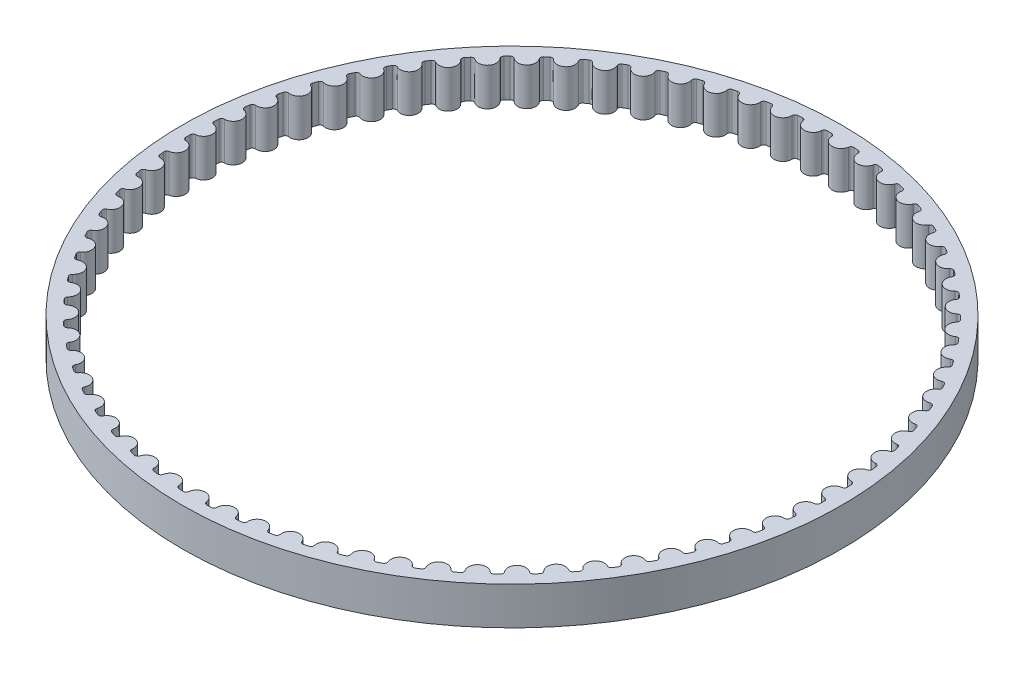
SolidWorks part; units mm, degrees
ref_plane "Front Plane" through (0, 0, 0) normal (0, 0, 1) x (1, 0, 0)
ref_plane "Top Plane" through (0, 0, 0) normal (0, 1, 0) x (1, 0, 0)
ref_plane "Right Plane" through (0, 0, 0) normal (1, 0, 0) x (0, 0, -1)
sketch "Sketch1" plane through (0, 0, 0) normal (0, 1, 0) x (1, 0, 0)
  circle A0 centre (0, 0) radius 34.819
  arc B0 (-1.7179, -33.475) -> (-1.2473, -33.4958) centre (0, 0) ccw
  arc B1 (-1.2473, -33.4958) -> (-0.9389, -33.2286) centre (-1.2362, -33.197) ccw
  arc B2 (0.9389, -33.2286) -> (-0.9389, -33.2286) centre (0, -33.3285) ccw
  arc B3 (0.9389, -33.2286) -> (1.2473, -33.4958) centre (1.2362, -33.197) ccw
  arc B4 (1.2473, -33.4958) -> (1.7179, -33.475) centre (0, 0) ccw
  arc B5 (1.7179, -33.475) -> (2.0015, -33.1816) centre (1.7026, -33.1763) ccw
  arc B6 (3.872, -33.0156) -> (2.0015, -33.1816) centre (2.9456, -33.1981) ccw
  arc B7 (3.872, -33.0156) -> (4.2028, -33.2545) centre (4.1653, -32.9578) ccw
  arc B8 (4.2028, -33.2545) -> (4.6697, -33.1921) centre (0, 0) ccw
  arc B9 (4.6697, -33.1921) -> (4.9263, -32.8748) centre (4.628, -32.896) ccw
  arc B10 (6.7747, -32.5442) -> (4.9263, -32.8748) centre (5.8681, -32.8078) ccw
  arc B11 (6.7747, -32.5442) -> (7.1254, -32.7529) centre (7.0619, -32.4607) ccw
  arc B12 (7.1254, -32.7529) -> (7.5849, -32.6495) centre (0, 0) ccw
  arc B13 (7.5849, -32.6495) -> (7.8125, -32.3108) centre (7.5173, -32.3583) ccw
  arc B14 (9.6245, -31.8181) -> (7.8125, -32.3108) centre (8.7447, -32.1608) ccw
  arc B15 (9.6245, -31.8181) -> (9.9922, -31.995) centre (9.9031, -31.7096) ccw
  arc B16 (9.9922, -31.995) -> (10.4408, -31.8514) centre (0, 0) ccw
  arc B17 (10.4408, -31.8514) -> (10.6375, -31.4939) centre (10.3477, -31.5673) ccw
  arc B18 (12.3989, -30.843) -> (10.6375, -31.4939) centre (11.5529, -31.2621) ccw
  arc B19 (12.3989, -30.843) -> (12.7809, -30.9867) centre (12.6668, -30.7103) ccw
  arc B20 (12.7809, -30.9867) -> (13.215, -30.804) centre (0, 0) ccw
  arc B21 (13.215, -30.804) -> (13.3794, -30.4305) centre (13.0971, -30.5292) ccw
  arc B22 (15.0763, -29.6265) -> (13.3794, -30.4305) centre (14.2706, -30.1188) ccw
  arc B23 (15.0763, -29.6265) -> (15.4694, -29.7358) centre (15.3315, -29.4706) ccw
  arc B24 (15.4694, -29.7358) -> (15.8858, -29.5155) centre (0, 0) ccw
  arc B25 (15.8858, -29.5155) -> (16.0164, -29.129) centre (15.744, -29.2522) ccw
  arc B26 (17.6357, -28.1781) -> (16.0164, -29.129) centre (16.8767, -28.7397) ccw
  arc B27 (17.6357, -28.1781) -> (18.037, -28.2523) centre (17.8761, -28.0003) ccw
  arc B28 (18.037, -28.2523) -> (18.4322, -27.996) centre (0, 0) ccw
  arc B29 (18.4322, -27.996) -> (18.5282, -27.5994) centre (18.2678, -27.7463) ccw
  arc B30 (20.0571, -26.5092) -> (18.5282, -27.5994) centre (19.3506, -27.1356) ccw
  arc B31 (20.0571, -26.5092) -> (20.4633, -26.5476) centre (20.2808, -26.3108) ccw
  arc B32 (20.4633, -26.5476) -> (20.8343, -26.2575) centre (0, 0) ccw
  arc B33 (20.8343, -26.2575) -> (20.8949, -25.8539) centre (20.6485, -26.0232) ccw
  arc B34 (22.3215, -24.6328) -> (20.8949, -25.8539) centre (21.6732, -25.3192) ccw
  arc B35 (22.3215, -24.6328) -> (22.7295, -24.6352) centre (22.5268, -24.4154) ccw
  arc B36 (22.7295, -24.6352) -> (23.0734, -24.3134) centre (0, 0) ccw
  arc B37 (23.0734, -24.3134) -> (23.0981, -23.906) centre (22.8676, -24.0965) ccw
  arc B38 (24.4112, -22.5636) -> (23.0981, -23.906) centre (23.8261, -23.3047) ccw
  arc B39 (24.4112, -22.5636) -> (24.8178, -22.5299) centre (24.5965, -22.329) ccw
  arc B40 (24.8178, -22.5299) -> (25.132, -22.179) centre (0, 0) ccw
  arc B41 (25.132, -22.179) -> (25.1206, -21.7711) centre (24.9078, -21.9811) ccw
  arc B42 (26.3098, -20.3179) -> (25.1206, -21.7711) centre (25.7925, -21.1077) ccw
  arc B43 (26.3098, -20.3179) -> (26.7119, -20.2484) centre (26.4736, -20.0677) ccw
  arc B44 (26.7119, -20.2484) -> (26.9938, -19.871) centre (0, 0) ccw
  arc B45 (26.9938, -19.871) -> (26.9464, -19.4657) centre (26.753, -19.6938) ccw
  arc B46 (28.0026, -17.9131) -> (26.9464, -19.4657) centre (27.5571, -18.7456) ccw
  arc B47 (28.0026, -17.9131) -> (28.397, -17.8083) centre (28.1436, -17.6495) ccw
  arc B48 (28.397, -17.8083) -> (28.6444, -17.4076) centre (0, 0) ccw
  arc B49 (28.6444, -17.4076) -> (28.5613, -17.008) centre (28.3889, -17.2523) ccw
  arc B50 (29.4761, -15.3681) -> (28.5613, -17.008) centre (29.106, -16.2367) ccw
  arc B51 (29.4761, -15.3681) -> (29.8597, -15.2289) centre (29.5934, -15.0931) ccw
  arc B52 (29.8597, -15.2289) -> (30.0708, -14.8078) centre (0, 0) ccw
  arc B53 (30.0708, -14.8078) -> (29.9527, -14.4172) centre (29.8025, -14.6758) ccw
  arc B54 (30.719, -12.7029) -> (29.9527, -14.4172) centre (30.4271, -13.6008) ccw
  arc B55 (30.719, -12.7029) -> (31.0888, -12.5303) centre (30.8115, -12.4185) ccw
  arc B56 (31.0888, -12.5303) -> (31.2618, -12.0922) centre (0, 0) ccw
  arc B57 (31.2618, -12.0922) -> (31.1097, -11.7136) centre (30.983, -11.9844) ccw
  arc B58 (31.7215, -9.9382) -> (31.1097, -11.7136) centre (31.5101, -10.8584) ccw
  arc B59 (31.7215, -9.9382) -> (32.0746, -9.7337) centre (31.7885, -9.6468) ccw
  arc B60 (32.0746, -9.7337) -> (32.2082, -9.282) centre (0, 0) ccw
  arc B61 (32.2082, -9.282) -> (32.0232, -8.9183) centre (31.9209, -9.1992) ccw
  arc B62 (32.4757, -7.0958) -> (32.0232, -8.9183) centre (32.3464, -8.0311) ccw
  arc B63 (32.4757, -7.0958) -> (32.8093, -6.8608) centre (32.5167, -6.7996) ccw
  arc B64 (32.8093, -6.8608) -> (32.9025, -6.3991) centre (0, 0) ccw
  arc B65 (32.9025, -6.3991) -> (32.6861, -6.0531) centre (32.609, -6.342) ccw
  arc B66 (32.9758, -4.1978) -> (32.6861, -6.0531) centre (32.9296, -5.1409) ccw
  arc B67 (32.9758, -4.1978) -> (33.2873, -3.9343) centre (32.9904, -3.8992) ccw
  arc B68 (33.2873, -3.9343) -> (33.3393, -3.4661) centre (0, 0) ccw
  arc B69 (33.3393, -3.4661) -> (33.0932, -3.1407) centre (33.0419, -3.4352) ccw
  arc B70 (33.2177, -1.267) -> (33.0932, -3.1407) centre (33.2551, -2.2104) ccw
  arc B71 (33.2177, -1.267) -> (33.5048, -0.9769) centre (33.2059, -0.9682) ccw
  arc B72 (33.5048, -0.9769) -> (33.5152, -0.506) centre (0, 0) ccw
  arc B73 (33.5152, -0.506) -> (33.2413, -0.2036) centre (33.2162, -0.5015) ccw
  arc B74 (33.1997, 1.6738) -> (33.2413, -0.2036) centre (33.3203, 0.7373) ccw
  arc B75 (33.1997, 1.6738) -> (33.46, 1.988) centre (33.1615, 1.9703) ccw
  arc B76 (33.46, 1.988) -> (33.4288, 2.458) centre (0, 0) ccw
  arc B77 (33.4288, 2.458) -> (33.1292, 2.7351) centre (33.1306, 2.4361) ccw
  arc B78 (32.9219, 4.6014) -> (33.1292, 2.7351) centre (33.1248, 3.6793) ccw
  arc B79 (32.9219, 4.6014) -> (33.1534, 4.9375) centre (32.8576, 4.8934) ccw
  arc B80 (33.1534, 4.9375) -> (33.0807, 5.4028) centre (0, 0) ccw
  arc B81 (33.0807, 5.4028) -> (32.7578, 5.6523) centre (32.7856, 5.3546) ccw
  arc B82 (32.3864, 7.493) -> (32.7578, 5.6523) centre (32.67, 6.5924) ccw
  arc B83 (32.3864, 7.493) -> (32.5872, 7.8482) centre (32.2966, 7.7782) ccw
  arc B84 (32.5872, 7.8482) -> (32.4738, 8.3054) centre (0, 0) ccw
  arc B85 (32.4738, 8.3054) -> (32.1301, 8.5254) centre (32.1841, 8.2313) ccw
  arc B86 (31.5974, 10.326) -> (32.1301, 8.5254) centre (31.9595, 9.454) ccw
  arc B87 (31.5974, 10.326) -> (31.7661, 10.6976) centre (31.4827, 10.6022) ccw
  arc B88 (31.7661, 10.6976) -> (31.6126, 11.1429) centre (0, 0) ccw
  arc B89 (31.6126, 11.1429) -> (31.2509, 11.3317) centre (31.3307, 11.0435) ccw
  arc B90 (30.5611, 13.0782) -> (31.2509, 11.3317) centre (30.9989, 12.2416) ccw
  arc B91 (30.5611, 13.0782) -> (30.6963, 13.4632) centre (30.4225, 13.3431) ccw
  arc B92 (30.6963, 13.4632) -> (30.5041, 13.8932) centre (0, 0) ccw
  arc B93 (30.5041, 13.8932) -> (30.1271, 14.0493) centre (30.232, 13.7693) ccw
  arc B94 (29.2857, 15.728) -> (30.1271, 14.0493) centre (29.7957, 14.9334) ccw
  arc B95 (29.2857, 15.728) -> (29.3863, 16.1235) centre (29.1242, 15.9797) ccw
  arc B96 (29.3863, 16.1235) -> (29.1569, 16.5348) centre (0, 0) ccw
  arc B97 (29.1569, 16.5348) -> (28.7675, 16.6569) centre (28.8968, 16.3873) ccw
  arc B98 (27.7811, 18.2547) -> (28.7675, 16.6569) centre (28.3593, 17.5083) ccw
  arc B99 (27.7811, 18.2547) -> (27.8464, 18.6576) centre (27.598, 18.4911) ccw
  arc B100 (27.8464, 18.6576) -> (27.5814, 19.047) centre (0, 0) ccw
  arc B101 (27.5814, 19.047) -> (27.1828, 19.1342) centre (27.3354, 18.8771) ccw
  arc B102 (26.059, 20.6386) -> (27.1828, 19.1342) centre (26.7009, 19.9462) ccw
  arc B103 (26.059, 20.6386) -> (26.0884, 21.0456) centre (25.8557, 20.8579) ccw
  arc B104 (26.0884, 21.0456) -> (25.7901, 21.4101) centre (0, 0) ccw
  arc B105 (25.7901, 21.4101) -> (25.3853, 21.4618) centre (25.5601, 21.2191) ccw
  arc B106 (24.133, 22.8609) -> (25.3853, 21.4618) centre (24.8336, 22.228) ccw
  arc B107 (24.133, 22.8609) -> (24.1263, 23.2689) centre (23.9111, 23.0614) ccw
  arc B108 (24.1263, 23.2689) -> (23.797, 23.6057) centre (0, 0) ccw
  arc B109 (23.797, 23.6057) -> (23.3892, 23.6213) centre (23.5847, 23.3951) ccw
  arc B110 (22.0181, 24.9044) -> (23.3892, 23.6213) centre (22.7719, 24.3358) ccw
  arc B111 (22.0181, 24.9044) -> (21.9754, 25.3102) centre (21.7794, 25.0844) ccw
  arc B112 (21.9754, 25.3102) -> (21.6176, 25.6165) centre (0, 0) ccw
  arc B113 (21.6176, 25.6165) -> (21.21, 25.596) centre (21.4248, 25.388) ccw
  arc B114 (19.7309, 26.7529) -> (21.21, 25.596) centre (20.532, 26.2531) ccw
  arc B115 (19.7309, 26.7529) -> (19.6525, 27.1533) centre (19.4772, 26.9111) ccw
  arc B116 (19.6525, 27.1533) -> (19.269, 27.4268) centre (0, 0) ccw
  arc B117 (19.269, 27.4268) -> (18.8649, 27.3704) centre (19.0971, 27.1821) ccw
  arc B118 (17.2892, 28.392) -> (18.8649, 27.3704) centre (18.1314, 27.965) ccw
  arc B119 (17.2892, 28.392) -> (17.1758, 28.784) centre (17.0226, 28.5272) ccw
  arc B120 (17.1758, 28.784) -> (16.7696, 29.0225) centre (0, 0) ccw
  arc B121 (16.7696, 29.0225) -> (16.372, 28.9306) centre (16.62, 28.7636) ccw
  arc B122 (14.7123, 29.8089) -> (16.372, 28.9306) centre (15.5889, 29.458) ccw
  arc B123 (14.7123, 29.8089) -> (14.5646, 30.1893) centre (14.4347, 29.92) ccw
  arc B124 (14.5646, 30.1893) -> (14.139, 30.391) centre (0, 0) ccw
  arc B125 (14.139, 30.391) -> (13.7511, 30.2643) centre (14.0129, 30.1199) ccw
  arc B126 (12.0202, 30.9925) -> (13.7511, 30.2643) centre (12.9244, 30.7205) ccw
  arc B127 (12.0202, 30.9925) -> (11.8395, 31.3584) centre (11.7339, 31.0787) ccw
  arc B128 (11.8395, 31.3584) -> (11.3977, 31.5217) centre (0, 0) ccw
  arc B129 (11.3977, 31.5217) -> (11.0225, 31.3612) centre (11.296, 31.2405) ccw
  arc B130 (9.2341, 31.9336) -> (11.0225, 31.3612) centre (10.1587, 31.7426) ccw
  arc B131 (9.2341, 31.9336) -> (9.0217, 32.2821) centre (8.9412, 31.9941) ccw
  arc B132 (9.0217, 32.2821) -> (8.5672, 32.4057) centre (0, 0) ccw
  arc B133 (8.5672, 32.4057) -> (8.2077, 32.2127) centre (8.4908, 32.1166) ccw
  arc B134 (6.3756, 32.6247) -> (8.2077, 32.2127) centre (7.3136, 32.5162) ccw
  arc B135 (6.3756, 32.6247) -> (6.1333, 32.9531) centre (6.0786, 32.6591) ccw
  arc B136 (6.1333, 32.9531) -> (5.6697, 33.036) centre (0, 0) ccw
  arc B137 (5.6697, 33.036) -> (5.3286, 32.812) centre (5.6191, 32.7413) ccw
  arc B138 (3.4673, 33.0606) -> (5.3286, 32.812) centre (4.4112, 33.0353) ccw
  arc B139 (3.4673, 33.0606) -> (3.1969, 33.3662) centre (3.1684, 33.0686) ccw
  arc B140 (3.1969, 33.3662) -> (2.7278, 33.4078) centre (0, 0) ccw
  arc B141 (2.7278, 33.4078) -> (2.4078, 33.1546) centre (2.7034, 33.1098) ccw
  arc B142 (0.5318, 33.2376) -> (2.4078, 33.1546) centre (1.4742, 33.2959) ccw
  arc B143 (0.5318, 33.2376) -> (0.2355, 33.5182) centre (0.2334, 33.2192) ccw
  arc B144 (0.2355, 33.5182) -> (-0.2355, 33.5182) centre (0, 0) ccw
  arc B145 (-0.2355, 33.5182) -> (-0.5318, 33.2376) centre (-0.2334, 33.2192) ccw
  arc B146 (-2.4078, 33.1546) -> (-0.5318, 33.2376) centre (-1.4742, 33.2959) ccw
  arc B147 (-2.4078, 33.1546) -> (-2.7278, 33.4078) centre (-2.7034, 33.1098) ccw
  arc B148 (-2.7278, 33.4078) -> (-3.1969, 33.3662) centre (0, 0) ccw
  arc B149 (-3.1969, 33.3662) -> (-3.4673, 33.0606) centre (-3.1684, 33.0686) ccw
  arc B150 (-5.3286, 32.812) -> (-3.4673, 33.0606) centre (-4.4112, 33.0353) ccw
  arc B151 (-5.3286, 32.812) -> (-5.6697, 33.036) centre (-5.6191, 32.7413) ccw
  arc B152 (-5.6697, 33.036) -> (-6.1333, 32.9531) centre (0, 0) ccw
  arc B153 (-6.1333, 32.9531) -> (-6.3756, 32.6247) centre (-6.0786, 32.6591) ccw
  arc B154 (-8.2077, 32.2127) -> (-6.3756, 32.6247) centre (-7.3136, 32.5162) ccw
  arc B155 (-8.2077, 32.2127) -> (-8.5672, 32.4057) centre (-8.4908, 32.1166) ccw
  arc B156 (-8.5672, 32.4057) -> (-9.0217, 32.2821) centre (0, 0) ccw
  arc B157 (-9.0217, 32.2821) -> (-9.2341, 31.9336) centre (-8.9412, 31.9941) ccw
  arc B158 (-11.0225, 31.3612) -> (-9.2341, 31.9336) centre (-10.1587, 31.7426) ccw
  arc B159 (-11.0225, 31.3612) -> (-11.3977, 31.5217) centre (-11.296, 31.2405) ccw
  arc B160 (-11.3977, 31.5217) -> (-11.8395, 31.3584) centre (0, 0) ccw
  arc B161 (-11.8395, 31.3584) -> (-12.0202, 30.9925) centre (-11.7339, 31.0787) ccw
  arc B162 (-13.7511, 30.2643) -> (-12.0202, 30.9925) centre (-12.9244, 30.7205) ccw
  arc B163 (-13.7511, 30.2643) -> (-14.139, 30.391) centre (-14.0129, 30.1199) ccw
  arc B164 (-14.139, 30.391) -> (-14.5646, 30.1893) centre (0, 0) ccw
  arc B165 (-14.5646, 30.1893) -> (-14.7123, 29.8089) centre (-14.4347, 29.92) ccw
  arc B166 (-16.372, 28.9306) -> (-14.7123, 29.8089) centre (-15.5889, 29.458) ccw
  arc B167 (-16.372, 28.9306) -> (-16.7696, 29.0225) centre (-16.62, 28.7636) ccw
  arc B168 (-16.7696, 29.0225) -> (-17.1758, 28.784) centre (0, 0) ccw
  arc B169 (-17.1758, 28.784) -> (-17.2892, 28.392) centre (-17.0226, 28.5272) ccw
  arc B170 (-18.8649, 27.3704) -> (-17.2892, 28.392) centre (-18.1314, 27.965) ccw
  arc B171 (-18.8649, 27.3704) -> (-19.269, 27.4268) centre (-19.0971, 27.1821) ccw
  arc B172 (-19.269, 27.4268) -> (-19.6525, 27.1533) centre (0, 0) ccw
  arc B173 (-19.6525, 27.1533) -> (-19.7309, 26.7529) centre (-19.4772, 26.9111) ccw
  arc B174 (-21.21, 25.596) -> (-19.7309, 26.7529) centre (-20.532, 26.2531) ccw
  arc B175 (-21.21, 25.596) -> (-21.6176, 25.6165) centre (-21.4248, 25.388) ccw
  arc B176 (-21.6176, 25.6165) -> (-21.9754, 25.3102) centre (0, 0) ccw
  arc B177 (-21.9754, 25.3102) -> (-22.0181, 24.9044) centre (-21.7794, 25.0844) ccw
  arc B178 (-23.3892, 23.6213) -> (-22.0181, 24.9044) centre (-22.7719, 24.3358) ccw
  arc B179 (-23.3892, 23.6213) -> (-23.797, 23.6057) centre (-23.5847, 23.3951) ccw
  arc B180 (-23.797, 23.6057) -> (-24.1263, 23.2689) centre (0, 0) ccw
  arc B181 (-24.1263, 23.2689) -> (-24.133, 22.8609) centre (-23.9111, 23.0614) ccw
  arc B182 (-25.3853, 21.4618) -> (-24.133, 22.8609) centre (-24.8336, 22.228) ccw
  arc B183 (-25.3853, 21.4618) -> (-25.7901, 21.4101) centre (-25.5601, 21.2191) ccw
  arc B184 (-25.7901, 21.4101) -> (-26.0884, 21.0456) centre (0, 0) ccw
  arc B185 (-26.0884, 21.0456) -> (-26.059, 20.6386) centre (-25.8557, 20.8579) ccw
  arc B186 (-27.1828, 19.1342) -> (-26.059, 20.6386) centre (-26.7009, 19.9462) ccw
  arc B187 (-27.1828, 19.1342) -> (-27.5814, 19.047) centre (-27.3354, 18.8771) ccw
  arc B188 (-27.5814, 19.047) -> (-27.8464, 18.6576) centre (0, 0) ccw
  arc B189 (-27.8464, 18.6576) -> (-27.7811, 18.2547) centre (-27.598, 18.4911) ccw
  arc B190 (-28.7675, 16.6569) -> (-27.7811, 18.2547) centre (-28.3593, 17.5083) ccw
  arc B191 (-28.7675, 16.6569) -> (-29.1569, 16.5348) centre (-28.8968, 16.3873) ccw
  arc B192 (-29.1569, 16.5348) -> (-29.3863, 16.1235) centre (0, 0) ccw
  arc B193 (-29.3863, 16.1235) -> (-29.2857, 15.728) centre (-29.1242, 15.9797) ccw
  arc B194 (-30.1271, 14.0493) -> (-29.2857, 15.728) centre (-29.7957, 14.9334) ccw
  arc B195 (-30.1271, 14.0493) -> (-30.5041, 13.8932) centre (-30.232, 13.7693) ccw
  arc B196 (-30.5041, 13.8932) -> (-30.6963, 13.4632) centre (0, 0) ccw
  arc B197 (-30.6963, 13.4632) -> (-30.5611, 13.0782) centre (-30.4225, 13.3431) ccw
  arc B198 (-31.2509, 11.3317) -> (-30.5611, 13.0782) centre (-30.9989, 12.2416) ccw
  arc B199 (-31.2509, 11.3317) -> (-31.6126, 11.1429) centre (-31.3307, 11.0435) ccw
  arc B200 (-31.6126, 11.1429) -> (-31.7661, 10.6976) centre (0, 0) ccw
  arc B201 (-31.7661, 10.6976) -> (-31.5974, 10.326) centre (-31.4827, 10.6022) ccw
  arc B202 (-32.1301, 8.5254) -> (-31.5974, 10.326) centre (-31.9595, 9.454) ccw
  arc B203 (-32.1301, 8.5254) -> (-32.4738, 8.3054) centre (-32.1841, 8.2313) ccw
  arc B204 (-32.4738, 8.3054) -> (-32.5872, 7.8482) centre (0, 0) ccw
  arc B205 (-32.5872, 7.8482) -> (-32.3864, 7.493) centre (-32.2966, 7.7782) ccw
  arc B206 (-32.7578, 5.6523) -> (-32.3864, 7.493) centre (-32.67, 6.5924) ccw
  arc B207 (-32.7578, 5.6523) -> (-33.0807, 5.4028) centre (-32.7856, 5.3546) ccw
  arc B208 (-33.0807, 5.4028) -> (-33.1534, 4.9375) centre (0, 0) ccw
  arc B209 (-33.1534, 4.9375) -> (-32.9219, 4.6014) centre (-32.8576, 4.8934) ccw
  arc B210 (-33.1292, 2.7351) -> (-32.9219, 4.6014) centre (-33.1248, 3.6793) ccw
  arc B211 (-33.1292, 2.7351) -> (-33.4288, 2.458) centre (-33.1306, 2.4361) ccw
  arc B212 (-33.4288, 2.458) -> (-33.46, 1.988) centre (0, 0) ccw
  arc B213 (-33.46, 1.988) -> (-33.1997, 1.6738) centre (-33.1615, 1.9703) ccw
  arc B214 (-33.2413, -0.2036) -> (-33.1997, 1.6738) centre (-33.3203, 0.7373) ccw
  arc B215 (-33.2413, -0.2036) -> (-33.5152, -0.506) centre (-33.2162, -0.5015) ccw
  arc B216 (-33.5152, -0.506) -> (-33.5048, -0.9769) centre (0, 0) ccw
  arc B217 (-33.5048, -0.9769) -> (-33.2177, -1.267) centre (-33.2059, -0.9682) ccw
  arc B218 (-33.0932, -3.1407) -> (-33.2177, -1.267) centre (-33.2551, -2.2104) ccw
  arc B219 (-33.0932, -3.1407) -> (-33.3393, -3.4661) centre (-33.0419, -3.4352) ccw
  arc B220 (-33.3393, -3.4661) -> (-33.2873, -3.9343) centre (0, 0) ccw
  arc B221 (-33.2873, -3.9343) -> (-32.9758, -4.1978) centre (-32.9904, -3.8992) ccw
  arc B222 (-32.6861, -6.0531) -> (-32.9758, -4.1978) centre (-32.9296, -5.1409) ccw
  arc B223 (-32.6861, -6.0531) -> (-32.9025, -6.3991) centre (-32.609, -6.342) ccw
  arc B224 (-32.9025, -6.3991) -> (-32.8093, -6.8608) centre (0, 0) ccw
  arc B225 (-32.8093, -6.8608) -> (-32.4757, -7.0958) centre (-32.5167, -6.7996) ccw
  arc B226 (-32.0232, -8.9183) -> (-32.4757, -7.0958) centre (-32.3464, -8.0311) ccw
  arc B227 (-32.0232, -8.9183) -> (-32.2082, -9.282) centre (-31.9209, -9.1992) ccw
  arc B228 (-32.2082, -9.282) -> (-32.0746, -9.7337) centre (0, 0) ccw
  arc B229 (-32.0746, -9.7337) -> (-31.7215, -9.9382) centre (-31.7885, -9.6468) ccw
  arc B230 (-31.1097, -11.7136) -> (-31.7215, -9.9382) centre (-31.5101, -10.8584) ccw
  arc B231 (-31.1097, -11.7136) -> (-31.2618, -12.0922) centre (-30.983, -11.9844) ccw
  arc B232 (-31.2618, -12.0922) -> (-31.0888, -12.5303) centre (0, 0) ccw
  arc B233 (-31.0888, -12.5303) -> (-30.719, -12.7029) centre (-30.8115, -12.4185) ccw
  arc B234 (-29.9527, -14.4172) -> (-30.719, -12.7029) centre (-30.4271, -13.6008) ccw
  arc B235 (-29.9527, -14.4172) -> (-30.0708, -14.8078) centre (-29.8025, -14.6758) ccw
  arc B236 (-30.0708, -14.8078) -> (-29.8597, -15.2289) centre (0, 0) ccw
  arc B237 (-29.8597, -15.2289) -> (-29.4761, -15.3681) centre (-29.5934, -15.0931) ccw
  arc B238 (-28.5613, -17.008) -> (-29.4761, -15.3681) centre (-29.106, -16.2367) ccw
  arc B239 (-28.5613, -17.008) -> (-28.6444, -17.4076) centre (-28.3889, -17.2523) ccw
  arc B240 (-28.6444, -17.4076) -> (-28.397, -17.8083) centre (0, 0) ccw
  arc B241 (-28.397, -17.8083) -> (-28.0026, -17.9131) centre (-28.1436, -17.6495) ccw
  arc B242 (-26.9464, -19.4657) -> (-28.0026, -17.9131) centre (-27.5571, -18.7456) ccw
  arc B243 (-26.9464, -19.4657) -> (-26.9938, -19.871) centre (-26.753, -19.6938) ccw
  arc B244 (-26.9938, -19.871) -> (-26.7119, -20.2484) centre (0, 0) ccw
  arc B245 (-26.7119, -20.2484) -> (-26.3098, -20.3179) centre (-26.4736, -20.0677) ccw
  arc B246 (-25.1206, -21.7711) -> (-26.3098, -20.3179) centre (-25.7925, -21.1077) ccw
  arc B247 (-25.1206, -21.7711) -> (-25.132, -22.179) centre (-24.9078, -21.9811) ccw
  arc B248 (-25.132, -22.179) -> (-24.8178, -22.5299) centre (0, 0) ccw
  arc B249 (-24.8178, -22.5299) -> (-24.4112, -22.5636) centre (-24.5965, -22.329) ccw
  arc B250 (-23.0981, -23.906) -> (-24.4112, -22.5636) centre (-23.8261, -23.3047) ccw
  arc B251 (-23.0981, -23.906) -> (-23.0734, -24.3134) centre (-22.8676, -24.0965) ccw
  arc B252 (-23.0734, -24.3134) -> (-22.7295, -24.6352) centre (0, 0) ccw
  arc B253 (-22.7295, -24.6352) -> (-22.3215, -24.6328) centre (-22.5268, -24.4154) ccw
  arc B254 (-20.8949, -25.8539) -> (-22.3215, -24.6328) centre (-21.6732, -25.3192) ccw
  arc B255 (-20.8949, -25.8539) -> (-20.8343, -26.2575) centre (-20.6485, -26.0232) ccw
  arc B256 (-20.8343, -26.2575) -> (-20.4633, -26.5476) centre (0, 0) ccw
  arc B257 (-20.4633, -26.5476) -> (-20.0571, -26.5092) centre (-20.2808, -26.3108) ccw
  arc B258 (-18.5282, -27.5994) -> (-20.0571, -26.5092) centre (-19.3506, -27.1356) ccw
  arc B259 (-18.5282, -27.5994) -> (-18.4322, -27.996) centre (-18.2678, -27.7463) ccw
  arc B260 (-18.4322, -27.996) -> (-18.037, -28.2523) centre (0, 0) ccw
  arc B261 (-18.037, -28.2523) -> (-17.6357, -28.1781) centre (-17.8761, -28.0003) ccw
  arc B262 (-16.0164, -29.129) -> (-17.6357, -28.1781) centre (-16.8767, -28.7397) ccw
  arc B263 (-16.0164, -29.129) -> (-15.8858, -29.5155) centre (-15.744, -29.2522) ccw
  arc B264 (-15.8858, -29.5155) -> (-15.4694, -29.7358) centre (0, 0) ccw
  arc B265 (-15.4694, -29.7358) -> (-15.0763, -29.6265) centre (-15.3315, -29.4706) ccw
  arc B266 (-13.3794, -30.4305) -> (-15.0763, -29.6265) centre (-14.2706, -30.1188) ccw
  arc B267 (-13.3794, -30.4305) -> (-13.215, -30.804) centre (-13.0971, -30.5292) ccw
  arc B268 (-13.215, -30.804) -> (-12.7809, -30.9867) centre (0, 0) ccw
  arc B269 (-12.7809, -30.9867) -> (-12.3989, -30.843) centre (-12.6668, -30.7103) ccw
  arc B270 (-10.6375, -31.4939) -> (-12.3989, -30.843) centre (-11.5529, -31.2621) ccw
  arc B271 (-10.6375, -31.4939) -> (-10.4408, -31.8514) centre (-10.3477, -31.5673) ccw
  arc B272 (-10.4408, -31.8514) -> (-9.9922, -31.995) centre (0, 0) ccw
  arc B273 (-9.9922, -31.995) -> (-9.6245, -31.8181) centre (-9.9031, -31.7096) ccw
  arc B274 (-7.8125, -32.3108) -> (-9.6245, -31.8181) centre (-8.7447, -32.1608) ccw
  arc B275 (-7.8125, -32.3108) -> (-7.5849, -32.6495) centre (-7.5173, -32.3583) ccw
  arc B276 (-7.5849, -32.6495) -> (-7.1254, -32.7529) centre (0, 0) ccw
  arc B277 (-7.1254, -32.7529) -> (-6.7747, -32.5442) centre (-7.0619, -32.4607) ccw
  arc B278 (-4.9263, -32.8748) -> (-6.7747, -32.5442) centre (-5.8681, -32.8078) ccw
  arc B279 (-4.9263, -32.8748) -> (-4.6697, -33.1921) centre (-4.628, -32.896) ccw
  arc B280 (-4.6697, -33.1921) -> (-4.2028, -33.2545) centre (0, 0) ccw
  arc B281 (-4.2028, -33.2545) -> (-3.872, -33.0156) centre (-4.1653, -32.9578) ccw
  arc B282 (-2.0015, -33.1816) -> (-3.872, -33.0156) centre (-2.9456, -33.1981) ccw
  arc B283 (-2.0015, -33.1816) -> (-1.7179, -33.475) centre (-1.7026, -33.1763) ccw
  dimension "D1" = 1.3
sketch_block_instance "Block-71T GT2 Pulley-1"
sketch_block "Block-71T GT2 Pulley"
extrude "Boss-Extrude1" add sketch "Sketch1" along normal blind 4
